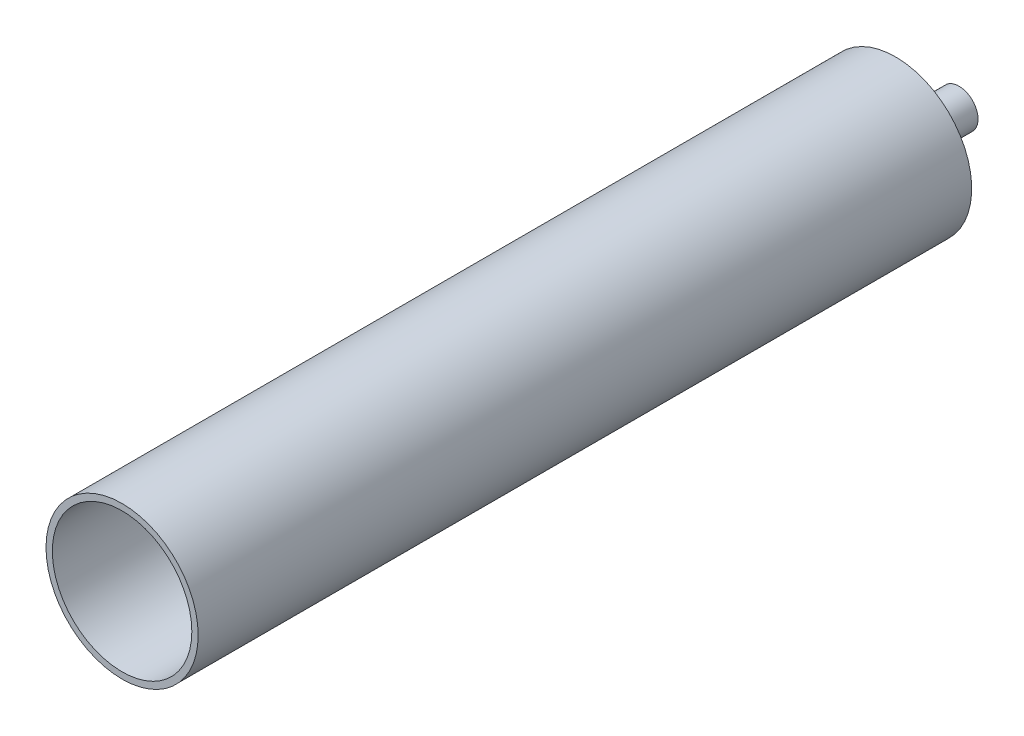
SolidWorks part; units mm, degrees
material "ABS PC"
ref_plane "Front" through (0, 0, 0) normal (0, 0, 1) x (1, 0, 0)
ref_plane "Top" through (0, 0, 0) normal (0, 1, 0) x (1, 0, 0)
ref_plane "Right" through (0, 0, 0) normal (1, 0, 0) x (0, 0, -1)
sketch "Sketch1" plane through (0, 0, 0) normal (0, 0, 1) x (1, 0, 0)
  circle A0 centre (0, 0) radius 7.62
  circle A1 centre (0, 0) radius 6.985
  dimension "D1" = 15.24
  dimension "D2" = 13.97
extrude "Boss-Extrude1" add sketch "Sketch1" along normal blind 76.2
sketch "Sketch2" plane through (0, 0, 0) normal (0, 0, -1) x (-1, 0, 0)
  circle A0 centre (0, 0) radius 7.62
extrude "Boss-Extrude2" add sketch "Sketch2" along normal blind 1.27
sketch "Sketch3" plane through (0, 0, -1.27) normal (0, 0, -1) x (-1, 0, 0)
  circle A0 centre (0, 0) radius 1.905
  circle A1 centre (0, 0) radius 1.27
  dimension "D1" = 3.81
  dimension "D2" = 2.54
extrude "Boss-Extrude3" add sketch "Sketch3" along normal blind 6.35 and the other way up to surface
sketch "Sketch4" plane through (0, 0, -1.27) normal (0, 0, -1) x (-1, 0, 0)
  circle A0 centre (0, 0) radius 1.27
  dimension "D1" = 2.54
extrude "Cut-Extrude1" cut sketch "Sketch4" against normal up to surface (1.27 mm away) up to face at (6.985, 0, 0)
